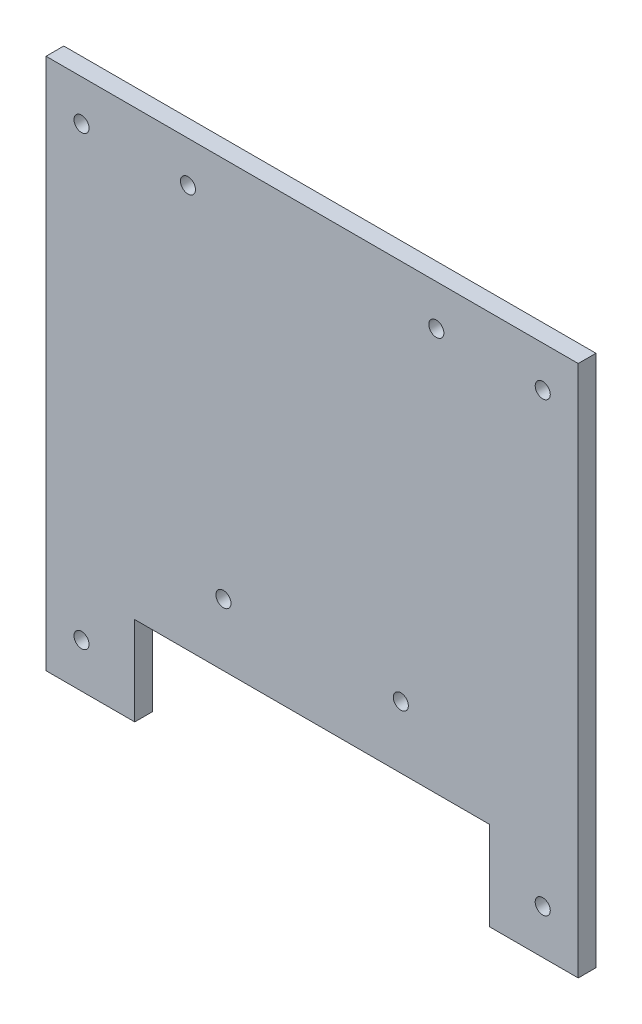
SolidWorks part; units mm, degrees
ref_plane "Alzado" through (0, 0, 0) normal (0, 0, 1) x (1, 0, 0)
ref_plane "Planta" through (0, 0, 0) normal (0, 1, 0) x (1, 0, 0)
ref_plane "Vista lateral" through (0, 0, 0) normal (1, 0, 0) x (0, 0, -1)
sketch "Croquis1" plane through (0, 0, 0) normal (0, 0, 1) x (1, 0, 0)
  line L0 (-300, 0) -> (-250, 0)
  line L1 (-250, 0) -> (-250, 50)
  line L2 (-300, 0) -> (-300, 300)
  line L3 (-300, 300) -> (0, 300)
  line L4 (0, 0) -> (0, 300)
  line L5 (-250, 50) -> (-50, 50)
  line L6 (-50, 50) -> (-50, 0)
  line L7 (-50, 0) -> (0, 0)
  dimension "D1" = 300
  dimension "D2" = 300
  dimension "D3" = 50
  dimension "D4" = 50
  dimension "D5" = 50
  dimension "D6" = 50
extrude "Saliente-Extruir1" add sketch "Croquis1" along normal blind 10
sketch "Croquis2" plane through (0, 0, 10) normal (0, 0, 1) x (1, 0, 0)
  line L0 (-300, 0) -> (-250, 0) construction
  line L1 (-300, 300) -> (-300, 0) construction
  line L2 (0, 300) -> (-300, 300) construction
  line L3 (0, 0) -> (0, 300) construction
  line L4 (-50, 0) -> (0, 0) construction
  circle A0 centre (-280, 25) radius 4.25
  circle A1 centre (-280, 277) radius 4.25
  circle A2 centre (-80, 277) radius 4.25
  circle A3 centre (-220, 277) radius 4.25
  circle A4 centre (-20, 277) radius 4.25
  circle A5 centre (-20, 25) radius 4.25
  circle A6 centre (120, 277) radius 4.25
  circle A7 centre (-420, 277) radius 4.25
  dimension "D1" = 8.5
  dimension "D9" = 8.5
  dimension "D11" = 8.5
  dimension "D2" = 25
  dimension "D3" = 20
  dimension "D4" = 23
  dimension "D5" = 20
  dimension "D6" = 25
  dimension "D7" = 200
  dimension "D8" = 200
  dimension "D10" = 200
  dimension "D12" = 200
extrude "Cortar-Extruir1" cut sketch "Croquis2" against normal through all
sketch "Croquis3" plane through (0, 0, 10) normal (0, 0, 1) x (1, 0, 0)
  line L0 (-250, 50) -> (-50, 50) construction
  line L4 (0, 0) -> (0, 300) construction
  line L5 (-300, 300) -> (-300, 0) construction
  circle A0 centre (-100, 85) radius 4.25
  circle A1 centre (-350, 85) radius 4.25
  circle A2 centre (-475, 85) radius 4.25
  circle A3 centre (50, 85) radius 4.25
  circle A4 centre (-200, 85) radius 4.25
  dimension "D1" = 8.5
  dimension "D2" = 35
  dimension "D3" = 250
  dimension "D4" = 100
  dimension "D5" = 100
  dimension "D6" = 250
  dimension "D7" = 125
extrude "Cortar-Extruir2" cut sketch "Croquis3" against normal through all
